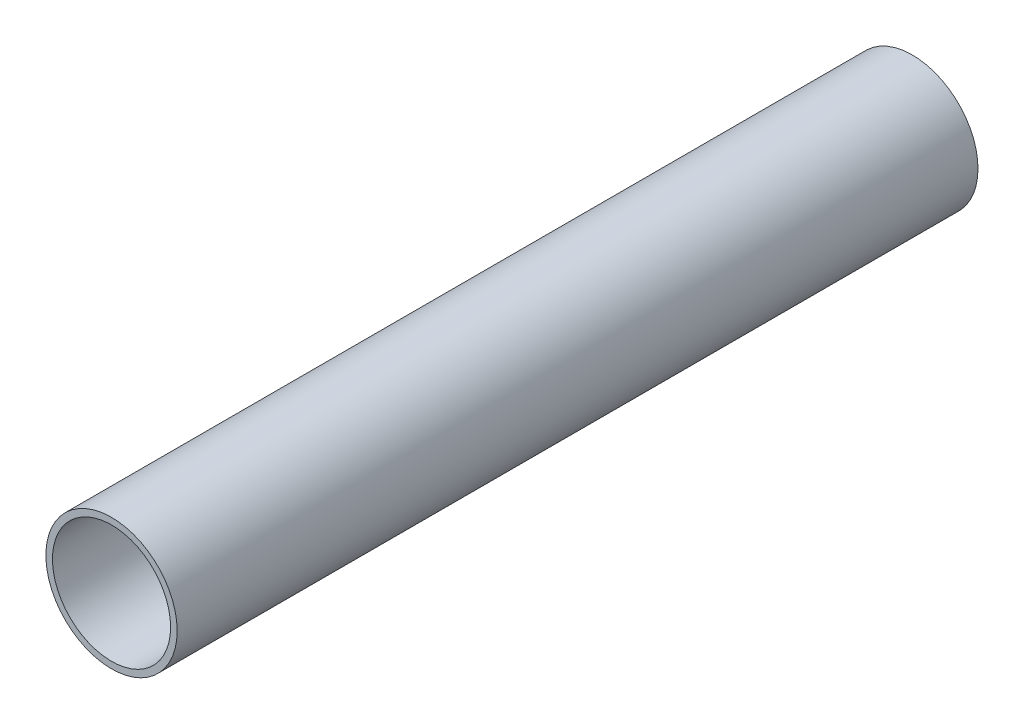
SolidWorks part; units mm, degrees
material "ABS"
ref_plane "Front Plane" through (0, 0, 0) normal (0, 0, 1) x (1, 0, 0)
ref_plane "Top Plane" through (0, 0, 0) normal (0, 1, 0) x (1, 0, 0)
ref_plane "Right Plane" through (0, 0, 0) normal (1, 0, 0) x (0, 0, -1)
sketch "Sketch3" plane through (0, 0, 0) normal (0, 0, 1) x (1, 0, 0)
  circle A0 centre (0, 0) radius 10
  dimension "D1" = 20
extrude "Extrude-Thin2" add sketch "Sketch3" along normal blind 122 thin contours A0 thin type one direction reverse wall 1
